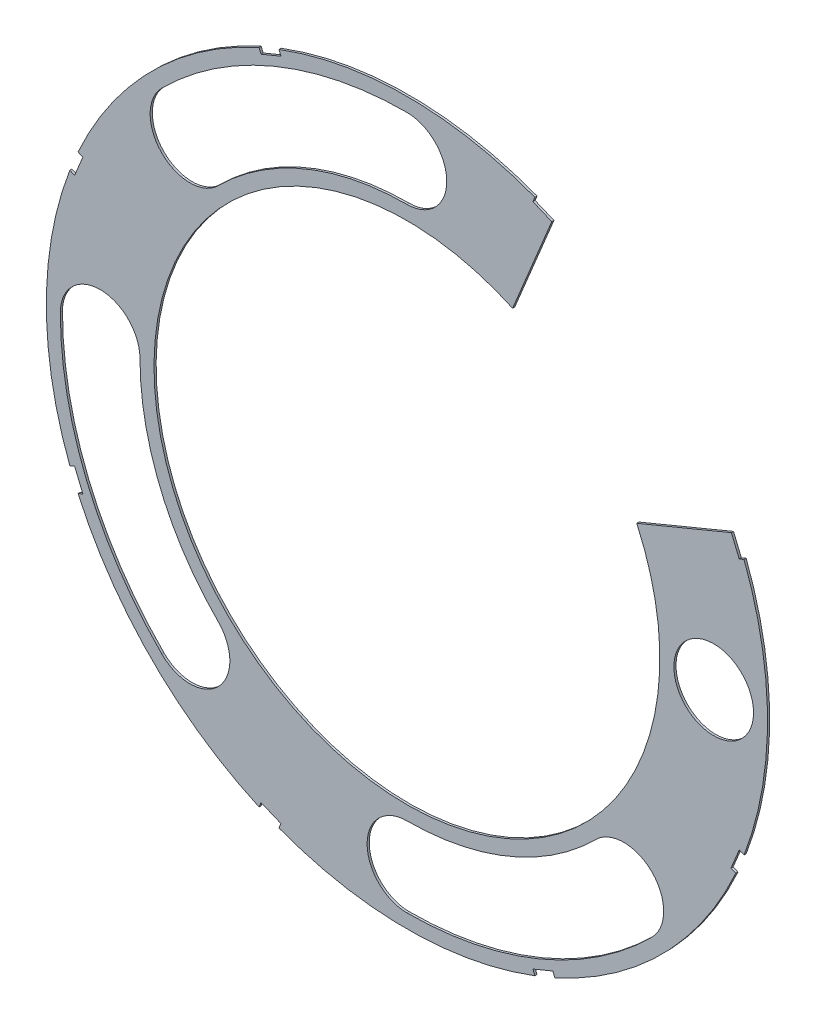
SolidWorks part; units mm, degrees
material "PTFE (general)"
ref_plane "Front Plane" through (0, 0, 0) normal (0, 0, 1) x (1, 0, 0)
ref_plane "Top Plane" through (0, 0, 0) normal (0, 1, 0) x (1, 0, 0)
ref_plane "Right Plane" through (0, 0, 0) normal (1, 0, 0) x (0, 0, -1)
sketch "Sketch4" plane through (0, 0, 0) normal (0, 0, 1) x (1, 0, 0)
  circle A0 centre (0, 0) radius 42.545
  dimension "D1" = 85.09
extrude "Boss-Extrude2" add sketch "Sketch4" along normal blind 0.254
sketch "Sketch5" plane through (0, 0, 0.254) normal (0, 0, 1) x (1, 0, 0)
  circle A0 centre (0, 0) radius 29.845
  circle A1 centre (0, 0) radius 42.545 construction
  dimension "D1" = 12.7
extrude "Cut-Extrude5" cut sketch "Sketch5" against normal through all
sketch "Sketch6" plane through (0, 0, 0.254) normal (0, 0, 1) x (1, 0, 0)
  line L0 (0, 0) -> (36.195, 0) construction
  line L1 (0, 0) -> (30.0839, -30.0839) construction
  line L2 (0, 0) -> (0, -42.545) construction
  line L3 (0, 0) -> (0, -42.545) construction
  line L4 (0, 0) -> (30.0839, -30.0839) construction
  line L5 (0, 0) -> (-30.0839, -30.0839) construction
  line L6 (0, 0) -> (-30.0839, -30.0839) construction
  line L7 (0, 0) -> (-42.545, 0) construction
  line L8 (0, 0) -> (-42.545, 0) construction
  line L9 (0, 0) -> (-30.0839, 30.0839) construction
  line L10 (0, 0) -> (-30.0839, 30.0839) construction
  line L11 (0, 0) -> (0, 42.545) construction
  line L12 (0, 0) -> (0, 42.545) construction
  line L13 (0, 0) -> (22.271, -22.271) construction
  line L14 (0, 0) -> (-22.271, -22.271) construction
  circle A0 centre (36.195, 0) radius 4.699
  circle A1 centre (0, 0) radius 42.545 construction
  arc A2 (28.9164, -28.9164) -> (22.271, -22.271) centre (25.5937, -25.5937) ccw
  arc A3 (22.271, -22.271) -> (0, -31.496) centre (0, 0) cw
  arc A4 (0, -31.496) -> (0, -40.894) centre (0, -36.195) ccw
  arc A5 (0, -40.894) -> (28.9164, -28.9164) centre (0, 0) ccw
  arc A6 (-28.9164, -28.9164) -> (-22.271, -22.271) centre (-25.5937, -25.5937) ccw
  arc A7 (-22.271, -22.271) -> (-31.496, 0) centre (0, 0) cw
  arc A8 (-40.894, 0) -> (-28.9164, -28.9164) centre (0, 0) ccw
  arc A9 (-31.496, 0) -> (-40.894, 0) centre (-36.195, 0) ccw
  arc A10 (-28.9164, 28.9164) -> (-22.271, 22.271) centre (-25.5937, 25.5937) ccw
  arc A11 (-22.271, 22.271) -> (0, 31.496) centre (0, 0) cw
  arc A12 (0, 40.894) -> (-28.9164, 28.9164) centre (0, 0) ccw
  arc A13 (0, 31.496) -> (0, 40.894) centre (0, 36.195) ccw
  circle A16 centre (0, 0) radius 29.845 construction
  point P4 (25.5937, -25.5937)
  point P11 (0, -36.195)
  point P13 (-25.5937, -25.5937)
  point P27 (-36.195, 0)
  point P30 (0, 0)
  point P36 (-25.5937, 25.5937)
  point P41 (0, 36.195)
  dimension "D2" = 9.398
  dimension "D3" = 45
  dimension "D4" = 90
  dimension "D1" = 6.35
  dimension "D6" = 6.35
  dimension "D7" = 9.398
  dimension "D8" = 4.699
  dimension "D9" = 4.699
  dimension "D5" = 6.35
  dimension "D10" = 90
extrude "Cut-Extrude6" cut sketch "Sketch6" against normal through all
sketch "Sketch8" plane through (0, 0, 0.254) normal (0, 0, 1) x (1, 0, 0)
  line L0 (0, 0) -> (39.3065, 16.2813) construction
  line L1 (0, 0) -> (16.2813, 39.3065) construction
  line L2 (39.2058, 14.8649) -> (38.2824, 17.0943)
  line L3 (16.2813, 39.3065) -> (15.1079, 39.7925)
  line L4 (14.8649, 39.2058) -> (17.0943, 38.2824)
  line L5 (15.1079, 39.7925) -> (14.8649, 39.2058)
  line L6 (0, 0) -> (42.545, 0) construction
  line L7 (-15.3509, 40.3791) -> (-17.6976, 39.4071)
  line L8 (-15.3509, 40.3791) -> (-14.8649, 39.2058)
  line L9 (-17.6976, 39.4071) -> (-17.2116, 38.2338)
  line L10 (-14.8649, 39.2058) -> (-17.2116, 38.2338)
  line L11 (-17.6976, 39.4071) -> (-14.8649, 39.2058) construction
  line L12 (-15.3509, 40.3791) -> (-17.2116, 38.2338) construction
  line L13 (-39.4071, 17.6976) -> (-40.3791, 15.3509)
  line L14 (-39.4071, 17.6976) -> (-38.2338, 17.2116)
  line L15 (-38.2338, 17.2116) -> (-39.2058, 14.8649)
  line L16 (-40.3791, 15.3509) -> (-39.2058, 14.8649)
  line L17 (-39.4071, 17.6976) -> (-39.2058, 14.8649) construction
  line L18 (-40.3791, 15.3509) -> (-38.2338, 17.2116) construction
  line L19 (-40.3791, -15.3509) -> (-39.4071, -17.6976)
  line L20 (-40.3791, -15.3509) -> (-39.2058, -14.8649)
  line L21 (-39.2058, -14.8649) -> (-38.2338, -17.2116)
  line L22 (-39.4071, -17.6976) -> (-38.2338, -17.2116)
  line L23 (-40.3791, -15.3509) -> (-38.2338, -17.2116) construction
  line L24 (-39.4071, -17.6976) -> (-39.2058, -14.8649) construction
  line L25 (-17.6976, -39.4071) -> (-15.3509, -40.3791)
  line L26 (-17.6976, -39.4071) -> (-17.2116, -38.2338)
  line L27 (-17.2116, -38.2338) -> (-14.8649, -39.2058)
  line L28 (-15.3509, -40.3791) -> (-14.8649, -39.2058)
  line L29 (-17.6976, -39.4071) -> (-14.8649, -39.2058) construction
  line L30 (-15.3509, -40.3791) -> (-17.2116, -38.2338) construction
  line L31 (15.3509, -40.3791) -> (17.6976, -39.4071)
  line L32 (15.3509, -40.3791) -> (14.8649, -39.2058)
  line L33 (14.8649, -39.2058) -> (17.2116, -38.2338)
  line L34 (17.6976, -39.4071) -> (17.2116, -38.2338)
  line L35 (15.3509, -40.3791) -> (17.2116, -38.2338) construction
  line L36 (17.6976, -39.4071) -> (14.8649, -39.2058) construction
  line L37 (39.4071, -17.6976) -> (40.3791, -15.3509)
  line L38 (39.4071, -17.6976) -> (38.2338, -17.2116)
  line L39 (38.2338, -17.2116) -> (39.2058, -14.8649)
  line L40 (40.3791, -15.3509) -> (39.2058, -14.8649)
  line L41 (39.4071, -17.6976) -> (39.2058, -14.8649) construction
  line L42 (40.3791, -15.3509) -> (38.2338, -17.2116) construction
  line L43 (27.1155, 12.4688) -> (38.2824, 17.0943)
  line L44 (39.3065, 16.2813) -> (39.7925, 15.1079)
  line L45 (17.0943, 38.2824) -> (12.4688, 27.1155)
  line L46 (39.7925, 15.1079) -> (39.2058, 14.8649)
  circle A0 centre (0, 0) radius 42.545 construction
  arc A1 (39.3065, 16.2813) -> (16.2813, 39.3065) centre (0, 0) ccw
  arc A2 (27.1155, 12.4688) -> (12.4688, 27.1155) centre (0, 0) ccw
  circle A4 centre (0, 0) radius 29.845 construction
  point P3 (-16.2813, 39.3065)
  point P11 (-39.3065, 16.2813)
  point P20 (-39.3065, -16.2813)
  point P25 (-16.2813, -39.3065)
  point P26 (0, 0)
  point P31 (16.2813, -39.3065)
  point P36 (39.3065, -16.2813)
  point P46 (0, 0)
  dimension "D2" = 67.5
  dimension "D3" = 22.5
  dimension "D4" = 1.27
  dimension "D5" = 1.27
  dimension "D6" = 2.54
  dimension "D7" = 1.27
  dimension "D8" = 0.635
  dimension "D9" = 0.635
  dimension "D10" = 112.5
  dimension "D12" = 1.27
  dimension "D13" = 0.635
  dimension "D14" = 0.635
  dimension "D15" = 2.413
  dimension "D16" = 90
  dimension "D17" = 270
  dimension "D18" = 90
  dimension "D19" = 2.413
  dimension "D20" = 270
  dimension "D21" = 22.5
  dimension "D11" = 6
extrude "Cut-Extrude11" cut sketch "Sketch8" against normal through all
